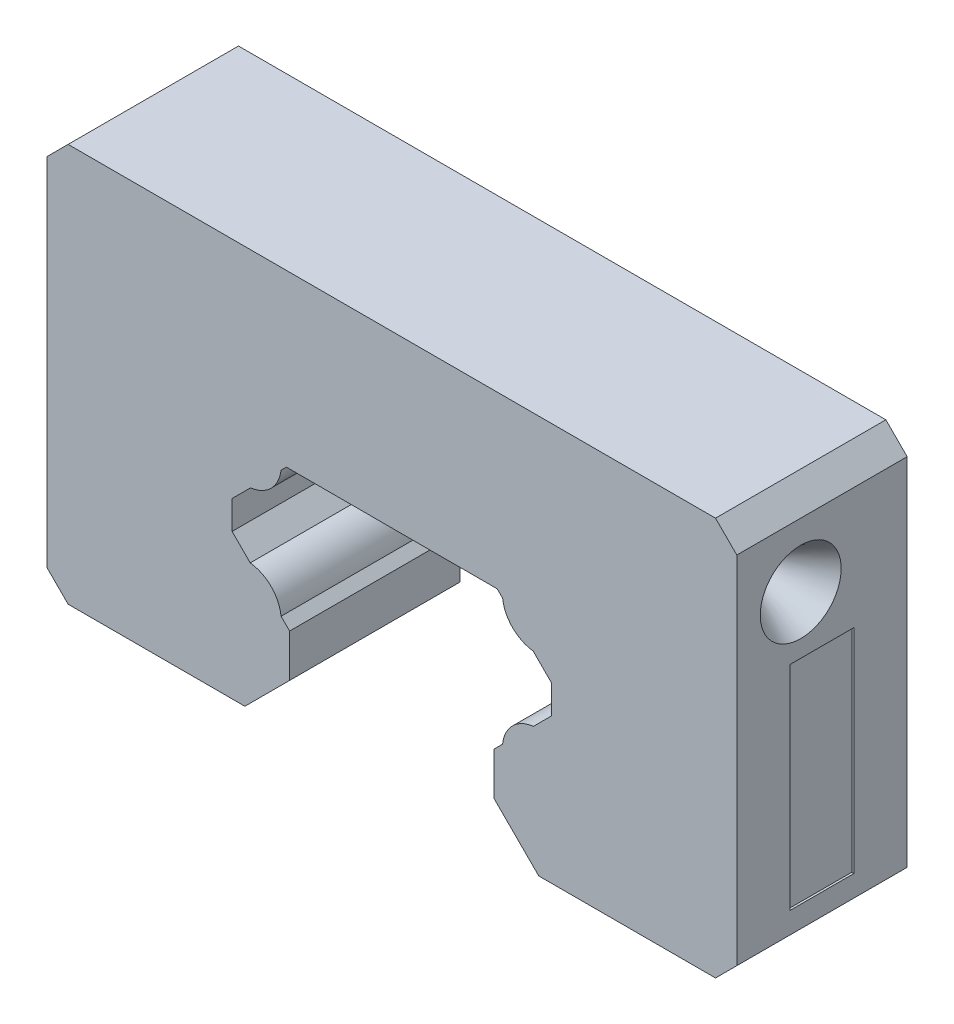
SolidWorks part; units mm, degrees
material "Настроенная пользователем пластмасса"
ref_plane "Спереди" through (0, 0, 0) normal (0, 0, 1) x (1, 0, 0)
ref_plane "Сверху" through (0, 0, 0) normal (0, 1, 0) x (1, 0, 0)
ref_plane "Справа" through (0, 0, 0) normal (1, 0, 0) x (0, 0, -1)
sketch "Model" plane through (0, 0, 0) normal (0, 0, 1) x (1, 0, 0)
  line L146 (4.7998, 2.0996) -> (6.8994, 0)
  line L147 (15.2, 0) -> (6.8994, 0)
  line L148 (16.2, 1) -> (15.2, 0)
  line L149 (16.2, 17.7) -> (16.2, 1)
  line L150 (15.2, 18.7) -> (16.2, 17.7)
  line L151 (-15.2, 18.7) -> (15.2, 18.7)
  line L152 (-16.2, 17.7) -> (-15.2, 18.7)
  line L153 (-16.2, 1) -> (-16.2, 17.7)
  line L154 (-15.2, 0) -> (-16.2, 1)
  line L155 (-6.8994, 0) -> (-15.2, 0)
  line L156 (-6.8994, 0) -> (-4.7998, 2.0996)
  line L157 (-4.7998, 2.0996) -> (-4.7998, 4.1091)
  line L158 (-4.7998, 4.1091) -> (-5.2008, 4.5101)
  line L159 (-6.6481, 5.9574) -> (-7.5, 6.8093)
  line L160 (-7.5, 6.8093) -> (-7.5, 8.1495)
  line L161 (-7.5, 8.1495) -> (-6.6345, 9.015)
  line L162 (-5.2023, 10.4472) -> (-4.9495, 10.7)
  line L163 (-4.9495, 10.7) -> (4.9495, 10.7)
  line L164 (4.9495, 10.7) -> (5.2023, 10.4472)
  line L165 (6.6345, 9.015) -> (7.5, 8.1495)
  line L166 (7.5, 8.1495) -> (7.5, 6.8093)
  line L167 (7.5, 6.8093) -> (6.6481, 5.9574)
  line L168 (5.2008, 4.5101) -> (4.7998, 4.1091)
  line L169 (4.7998, 4.1091) -> (4.7998, 2.0996)
  arc A13 (-5.2008, 4.5101) -> (-6.6481, 5.9574) centre (-6.8215, 4.3367) ccw
  arc A14 (-6.6345, 9.015) -> (-5.2023, 10.4472) centre (-6.8215, 10.6342) ccw
  arc A15 (5.2023, 10.4472) -> (6.6345, 9.015) centre (6.8215, 10.6342) ccw
  arc A16 (6.6481, 5.9574) -> (5.2008, 4.5101) centre (6.8215, 4.3367) ccw
extrude "Бобышка-Вытянуть1" add sketch "Model" along normal blind 8
sketch "Эскиз1" plane through (-16.2, 0, 0) normal (-1, 0, 0) x (0, 0, 1)
  line L1 (8, 18.7) -> (0, 18.7) construction
  line L2 (8, 17.7) -> (8, 1) construction
  circle A0 centre (5, 14.7) radius 1.9
  dimension "D1" = 3
  dimension "D2" = 4
extrude "Вырез-Вытянуть1" cut sketch "Эскиз1" against normal blind 3 draft 31
sketch "Эскиз2" plane through (16.2, 0, 0) normal (1, 0, 0) x (0, 0, -1)
  circle A0 centre (-5, 14.7) radius 1.9
extrude "Вырез-Вытянуть2" cut sketch "Эскиз2" against normal blind 3 draft 31
sketch "Эскиз3" plane through (-16.2, 0, 0) normal (-1, 0, 0) x (0, 0, 1)
  line L0 (4, 1) -> (4, 50001) construction
  line L1 (8, 1) -> (0, 1) construction
  line L2 (5.1102, 7) -> (50005.1102, 7) construction
  line L4 (2.5, 12) -> (5.5, 12)
  line L5 (2.5, 12) -> (2.5, 2)
  line L6 (2.5, 2) -> (5.5, 2)
  line L7 (5.5, 12) -> (5.5, 2)
  line L8 (2.5, 12) -> (5.5, 2) construction
  line L9 (2.5, 2) -> (5.5, 12) construction
  point P4 (4, 1)
  point P7 (4, 7)
  dimension "D1" = 6
  dimension "D2" = 10
  dimension "D3" = 3
extrude "Вырез-Вытянуть5" cut sketch "Эскиз3" against normal blind 0.1
sketch "Эскиз4" plane through (16.2, 0, 0) normal (1, 0, 0) x (0, 0, -1)
  line L1 (-5.5, 2) -> (-2.5, 2)
  line L2 (-5.5, 2) -> (-5.5, 12)
  line L3 (-5.5, 12) -> (-2.5, 12)
  line L4 (-2.5, 2) -> (-2.5, 12)
  line L5 (-5.5, 2) -> (-2.5, 12) construction
  line L6 (-5.5, 12) -> (-2.5, 2) construction
  point P0 (-4, 7)
extrude "Вырез-Вытянуть6" cut sketch "Эскиз4" against normal blind 0.1
sketch "Эскиз6" plane through (-16.1, 0, 0) normal (-1, 0, 0) x (0, 0, 1)
  line L0 (5.1467, 2) -> (5.1467, 12) construction
  line L1 (2.5, 2) -> (5.5, 2) construction
  line L2 (2.5, 12) -> (5.5, 12) construction
  text T0 "HC15" font "Century Gothic" height in points 8
extrude "Бобышка-Вытянуть2" add sketch "Эскиз6" along normal blind 0.1
